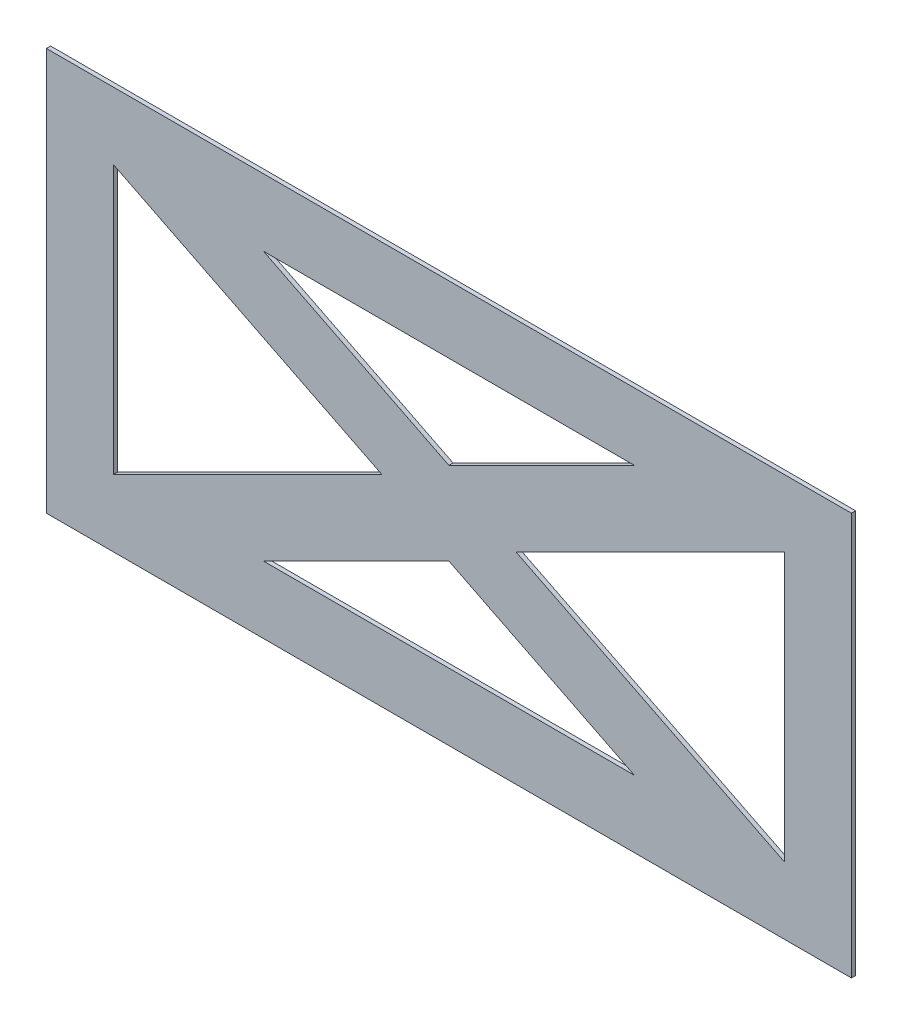
SolidWorks part; units mm, degrees
ref_plane "Front Plane" through (0, 0, 0) normal (0, 0, 1) x (1, 0, 0)
ref_plane "Top Plane" through (0, 0, 0) normal (0, 1, 0) x (1, 0, 0)
ref_plane "Right Plane" through (0, 0, 0) normal (1, 0, 0) x (0, 0, -1)
sketch "Sketch1" plane through (0, 0, 0) normal (0, 0, 1) x (1, 0, 0)
  line L0 (-127, 50.8) -> (-127, -50.8)
  line L1 (-152.4, -76.2) -> (152.4, -76.2)
  line L2 (-152.4, -76.2) -> (-152.4, 76.2)
  line L3 (-152.4, 76.2) -> (152.4, 76.2)
  line L4 (152.4, -76.2) -> (152.4, 76.2)
  line L5 (-152.4, -76.2) -> (152.4, 76.2) construction
  line L6 (-152.4, 76.2) -> (152.4, -76.2) construction
  line L7 (-127, -50.8) -> (-25.4, 0)
  line L8 (-25.4, 0) -> (-127, 50.8)
  line L9 (-70.2039, 50.8) -> (70.2039, 50.8)
  line L10 (70.2039, 50.8) -> (0, 15.6981)
  line L11 (0, 15.6981) -> (-70.2039, 50.8)
  line L12 (0, -15.6981) -> (-70.2039, -50.8)
  line L13 (-70.2039, -50.8) -> (70.2039, -50.8)
  line L14 (70.2039, -50.8) -> (0, -15.6981)
  line L15 (25.4, 0) -> (127, 50.8)
  line L16 (127, 50.8) -> (127, -50.8)
  line L17 (127, -50.8) -> (25.4, 0)
  point P0 (0, 0)
  dimension "D1" = 304.8
  dimension "D2" = 152.4
  dimension "D3" = 25.4
  dimension "D4" = 25.4
  dimension "D5" = 25.4
  dimension "D6" = 25.4
  dimension "D7" = 25.4
  dimension "D8" = 25.4
extrude "Boss-Extrude1" add sketch "Sketch1" along normal mid plane 1.5875
